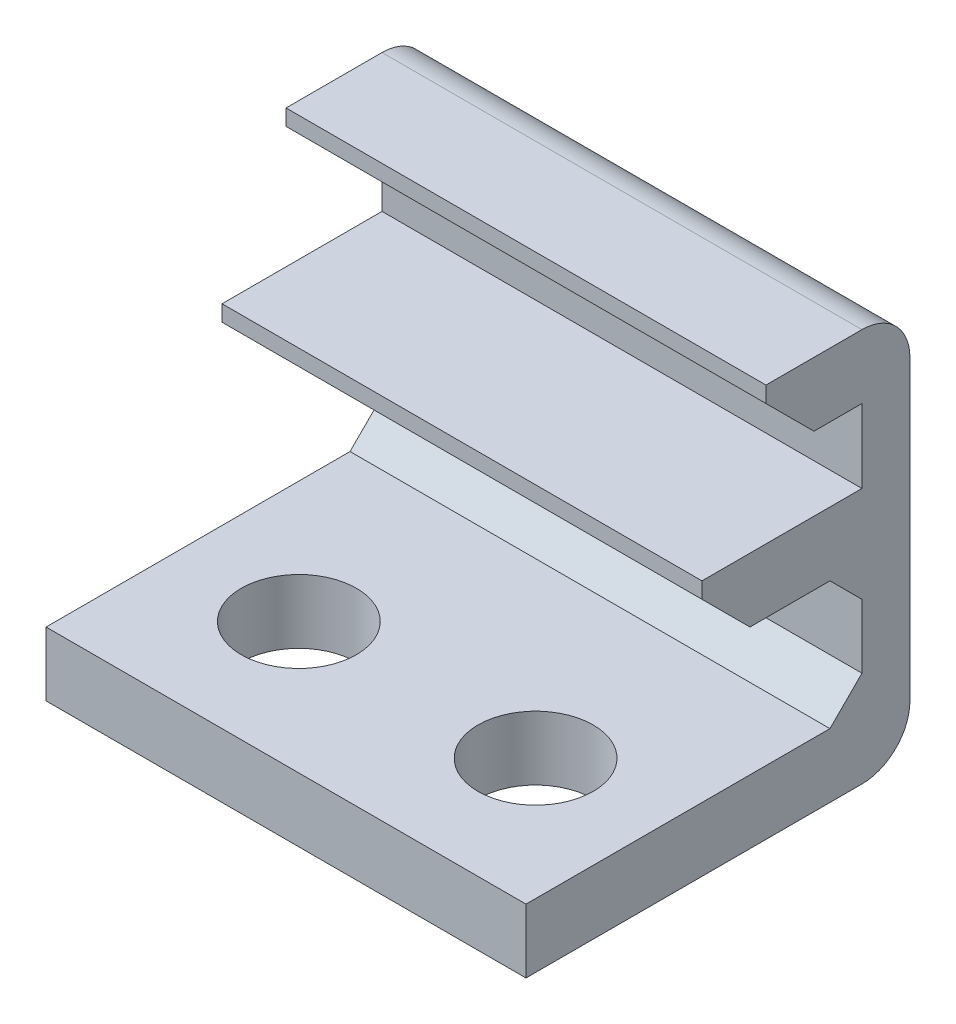
SolidWorks part; units mm, degrees
ref_plane "Plano frontal" through (0, 0, 0) normal (0, 0, 1) x (1, 0, 0)
ref_plane "Plano superior" through (0, 0, 0) normal (0, 1, 0) x (1, 0, 0)
ref_plane "Plano direito" through (0, 0, 0) normal (1, 0, 0) x (0, 0, -1)
sketch "Sketch1" plane through (0, 0, 0) normal (1, 0, 0) x (0, 0, -1)
  line L0 (-5.25, -4.15) -> (-5.25, -6.15)
  line L1 (2.25, 6.15) -> (6.75, 6.15)
  line L2 (2.25, 6.15) -> (2.25, 4.15)
  line L3 (-5.25, -6.15) -> (6.75, -6.15)
  line L4 (6.75, 6.15) -> (6.75, -6.15)
  line L5 (2.25, 4.15) -> (5.25, 4.15)
  line L7 (-5.25, -4.15) -> (5.25, -4.15)
  line L8 (5.25, 4.15) -> (5.25, 1.85)
  line L9 (5.25, -0.15) -> (5.25, -4.15)
  line L10 (0.25, 1.85) -> (5.25, 1.85)
  line L11 (0.25, 1.85) -> (0.25, -0.15)
  line L12 (0.25, -0.15) -> (5.25, -0.15)
  point P7 (6.75, 0)
  point P15 (0, -4.15)
  dimension "D1" = 8
  dimension "D2" = 12
  dimension "D3" = 1.5
  dimension "D4" = 2
  dimension "D5" = 2.3
  dimension "D6" = 4.5
  dimension "D7" = 5
  dimension "D8" = 4
  dimension "D9" = 10.3
extrude "Boss-Extrude1" add sketch "Sketch1" along normal mid plane 15 contours L5 L8 L7 L2 L3 L4 L1
chamfer "Chamfer1" distance 1 angle 45 2 edges at (0, -0.15, -5.25) (0, -4.15, -5.25)
sketch "Sketch2" plane through (0, -4.15, 0) normal (0, 1, 0) x (1, 0, 0)
  line L1 (-7.5, -5.25) -> (-7.5, 4.25) construction
  line L2 (0, -6.6) -> (0, 6.6) construction
  line L3 (7.5, -5.25) -> (-7.5, -5.25) construction
  circle A0 centre (-3.7, -1.15) radius 1.5 construction
  circle A1 centre (-3.7, -1.15) radius 1.8
  circle A2 centre (3.7, -1.15) radius 1.5 construction
  circle A3 centre (3.7, -1.15) radius 1.8
  dimension "D1" = 3
  dimension "D3" = 2
  dimension "D4" = 2.3
  dimension "D2" = 0.3
extrude "Cut-Extrude1" cut sketch "Sketch2" against normal through all and the other way blind 3
fillet "Fillet1" radius 1.5 2 edges at (0, -6.15, -6.75) (0, 6.15, -6.75)
chamfer "Chamfer2" distance 1.5 angle 45 2 edges at (0, -0.15, -0.25) (0, 4.15, -2.25)
